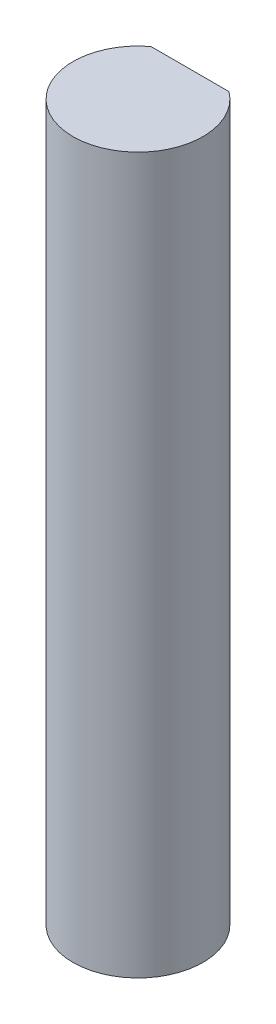
SolidWorks part; units mm, degrees
ref_plane "Front Plane" through (0, 0, 0) normal (0, 0, 1) x (1, 0, 0)
ref_plane "Top Plane" through (0, 0, 0) normal (0, 1, 0) x (1, 0, 0)
ref_plane "Right Plane" through (0, 0, 0) normal (1, 0, 0) x (0, 0, -1)
sketch "Sketch1" plane through (0, 0, 0) normal (0, 1, 0) x (1, 0, 0)
  line L0 (-1.905, 2.54) -> (1.905, 2.54)
  arc A0 (-1.905, 2.54) -> (1.905, 2.54) centre (0, 0) ccw
  dimension "D1" = 6.35
  dimension "D2" = 2.54
extrude "Boss-Extrude1" add sketch "Sketch1" along normal blind 34.925
